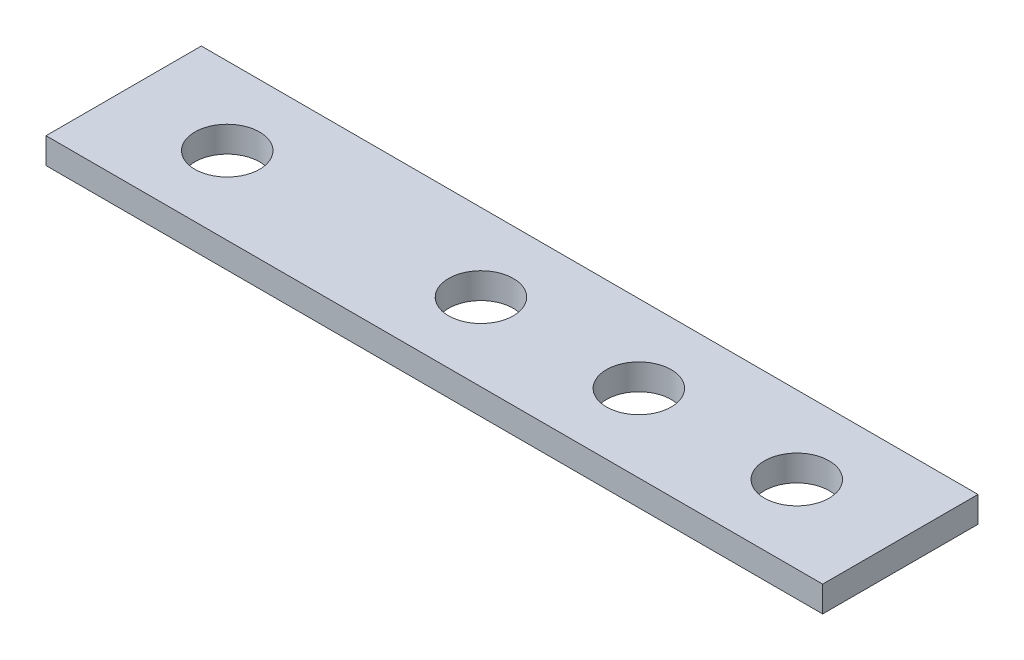
SolidWorks part; units mm, degrees
ref_plane "Front Plane" through (0, 0, 0) normal (0, 0, 1) x (1, 0, 0)
ref_plane "Top Plane" through (0, 0, 0) normal (0, 1, 0) x (1, 0, 0)
ref_plane "Right Plane" through (0, 0, 0) normal (1, 0, 0) x (0, 0, -1)
sketch "Sketch1" plane through (0, 0, 0) normal (0, 1, 0) x (1, 0, 0)
  line L1 (-30, -6) -> (30, -6)
  line L2 (-30, -6) -> (-30, 6)
  line L3 (-30, 6) -> (30, 6)
  line L4 (30, -6) -> (30, 6)
  line L5 (-30, -6) -> (30, 6) construction
  line L6 (-30, 6) -> (30, -6) construction
  point P0 (0, 0)
  dimension "D1" = 12
  dimension "D2" = 60
extrude "Boss-Extrude1" add sketch "Sketch1" along normal blind 2
sketch "Sketch2" plane through (0, 2, 0) normal (0, 1, 0) x (1, 0, 0)
  line L0 (30, -6) -> (30, 6) construction
  line L1 (-30, 6) -> (-30, -6) construction
  point P0 (22, 0)
  point P1 (9.8, 0)
  point P2 (-2.4, 0)
  point P3 (-22, 0)
  dimension "D1" = 8
  dimension "D2" = 12.2
  dimension "D3" = 12.2
  dimension "D4" = 8
hole_wizard "Ø5.0mm Dowel Hole1" positions "Sketch3" profile "Sketch4" hole size "Ø5.0" standard "ANSI Metric" end condition through all
sketch "Sketch3" plane through (0, 2, 0) normal (0, 1, 0) x (1, 0, 0)
  point P0 (22, 0)
  point P3 (9.8, 0)
  point P6 (-2.4, 0)
  point P9 (-22, 0)
sketch "Sketch4" plane through (22, 2, 0) normal (1, 0, 0) x (0, 0, 1)
  line L0 (0, 0) -> (0, 2)
  line L1 (0, 2) -> (2.5, 2)
  line L2 (2.5, 2) -> (2.5, 0)
  line L5 (2.5, 0) -> (0, 0)
  line L11 (0, -6.35) -> (0, 107.95) construction
  dimension "Thru Hole Dia." = 5
  dimension "Thru Hole Depth" = 2
